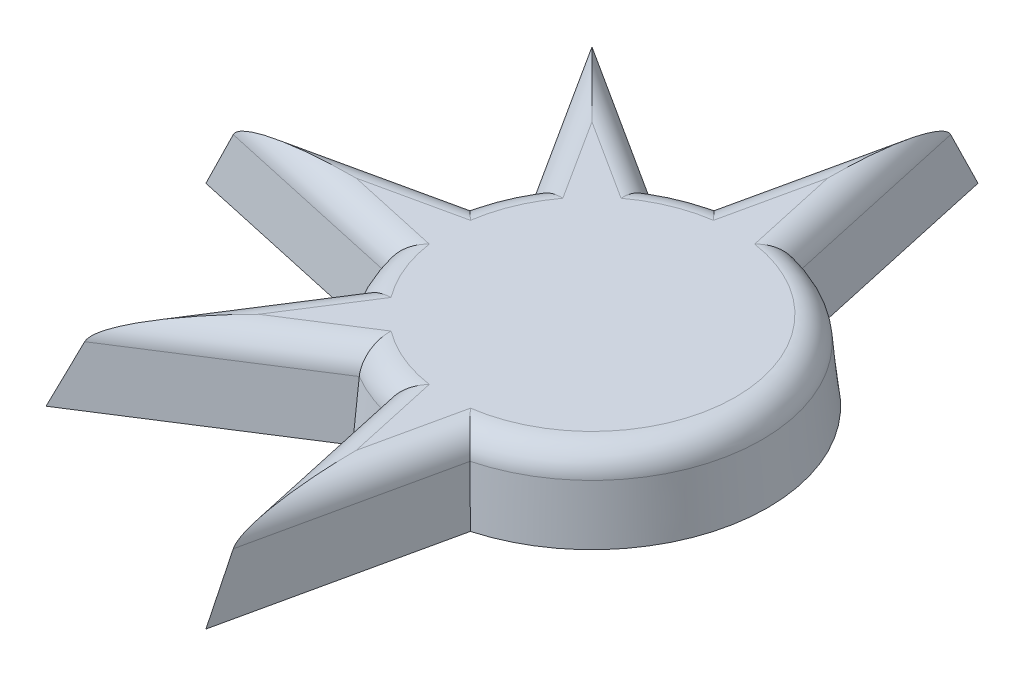
SolidWorks part; units mm, degrees
material "ABS"
ref_plane "Front Plane" through (0, 0, 0) normal (0, 0, 1) x (1, 0, 0)
ref_plane "Top Plane" through (0, 0, 0) normal (0, 1, 0) x (1, 0, 0)
ref_plane "Right Plane" through (0, 0, 0) normal (1, 0, 0) x (0, 0, -1)
sketch "Sketch1" plane through (0, 0, 0) normal (0, 1, 0) x (1, 0, 0)
  line L1 (-17.5, 17.5) -> (17.5, 17.5)
  line L2 (-17.5, 17.5) -> (-17.5, -17.5)
  line L3 (-17.5, -17.5) -> (17.5, -17.5)
  line L4 (17.5, 17.5) -> (17.5, -17.5)
  line L5 (-17.5, 17.5) -> (17.5, -17.5) construction
  line L6 (-17.5, -17.5) -> (17.5, 17.5) construction
  point P0 (0, 0)
  dimension "D1" = 35
sketch "Sketch2" plane through (0, 0, 0) normal (0, 1, 0) x (1, 0, 0)
  line L0 (0, 14.5436) -> (-1.795, 6.3768)
  line L1 (0, 14.5436) -> (0, 6.6246) construction
  line L2 (0, 14.5436) -> (1.795, 6.3768)
  line L9 (0, -14.5436) -> (1.795, -6.3768)
  line L10 (0, -14.5436) -> (-1.795, -6.3768)
  line L11 (-10.2839, -10.2839) -> (-3.2399, -5.7783)
  line L12 (-10.2839, -10.2839) -> (-5.7783, -3.2399)
  line L13 (-14.5436, 0) -> (-6.3768, -1.795)
  line L14 (-14.5436, 0) -> (-6.3768, 1.795)
  line L15 (-10.2839, 10.2839) -> (-5.7783, 3.2399)
  line L16 (-10.2839, 10.2839) -> (-3.2399, 5.7783)
  line L17 (10.2839, 10.2839) -> (5.7783, 3.2399) [skipped]
  line L18 (10.2839, 10.2839) -> (3.2399, 5.7783) [skipped]
  line L19 (14.5436, 0) -> (6.3768, 1.795) [skipped]
  line L20 (14.5436, 0) -> (6.3768, -1.795) [skipped]
  line L21 (10.2839, -10.2839) -> (5.7783, -3.2399) [skipped]
  line L22 (10.2839, -10.2839) -> (3.2399, -5.7783) [skipped]
  circle A0 centre (0, 0) radius 6.6246
  point P31 (0, 0)
  dimension "D1" = 8
extrude "Boss-Extrude1" add sketch "Sketch2" along normal blind 3 draft 6
fillet "Fillet1" radius 1 15 edges at (-9.5981, 3, -0.7641) (-5.8291, 3, -2.4145) (-7.3272, 3, -6.2466) (-6.2466, 3, -7.3272) (-2.4145, 3, -5.8291) (-0.7641, 3, -9.5981) (0.7641, 3, -9.5981) (6.3093, 3, 0) (0.7641, 3, 9.5981) (-0.7641, 3, 9.5981) (-2.4145, 3, 5.8291) (-6.2466, 3, 7.3272) (-7.3272, 3, 6.2466) (-5.8291, 3, 2.4145) (-9.5981, 3, 0.7641)
